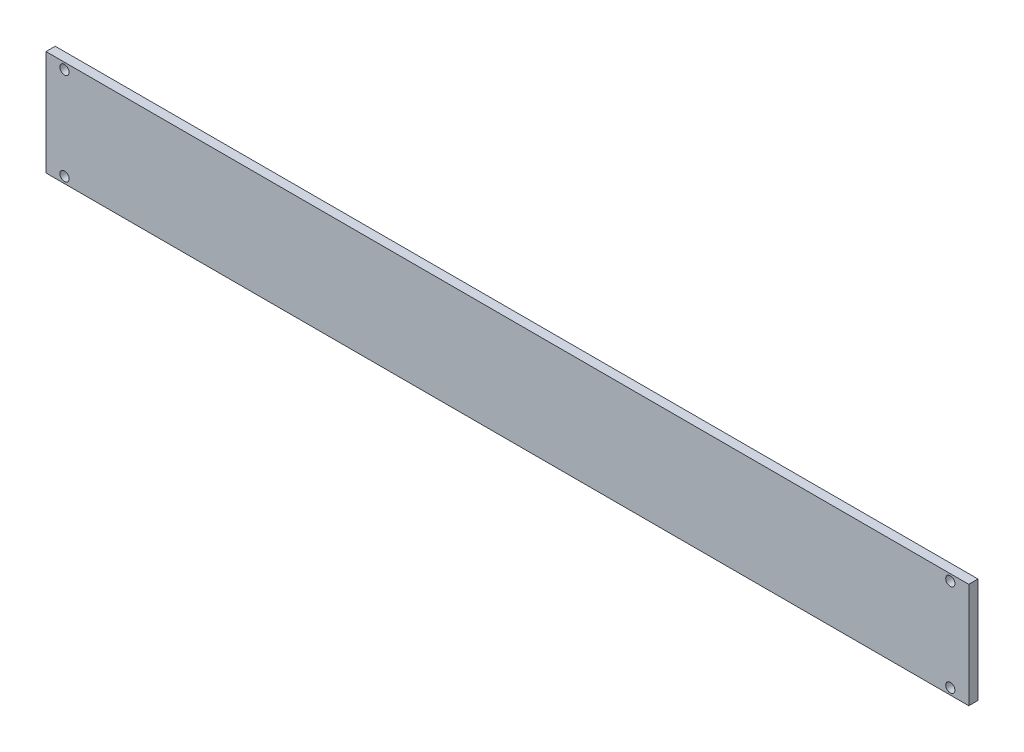
SolidWorks part; units mm, degrees
material "Faggio"
ref_plane "Piano frontale" through (0, 0, 0) normal (0, 0, 1) x (1, 0, 0)
ref_plane "Piano superiore" through (0, 0, 0) normal (0, 1, 0) x (1, 0, 0)
ref_plane "Piano destro" through (0, 0, 0) normal (1, 0, 0) x (0, 0, -1)
sketch "Schizzo1" plane through (0, 0, 0) normal (0, 0, 1) x (1, 0, 0)
  line L1 (-500, 57) -> (500, 57)
  line L2 (-500, 57) -> (-500, -57)
  line L3 (-500, -57) -> (500, -57)
  line L4 (500, 57) -> (500, -57)
  line L5 (-500, 57) -> (500, -57) construction
  line L6 (-500, -57) -> (500, 57) construction
  circle A0 centre (-480, 50) radius 5
  circle A1 centre (-480, -50) radius 5
  circle A2 centre (480, 50) radius 5
  circle A3 centre (480, -50) radius 5
  point P0 (0, 0)
  dimension "D3" = 10
  dimension "D8" = 10
  dimension "D9" = 10
  dimension "D1" = 1000
  dimension "D2" = 100
  dimension "D4" = 7
  dimension "D5" = 20
  dimension "D6" = 20
  dimension "D7" = 7
  dimension "D10" = 7
  dimension "D11" = 7
  dimension "D12" = 20
  dimension "D13" = 20
extrude "Estrusione-Estrusione1" add sketch "Schizzo1" along normal blind 10
